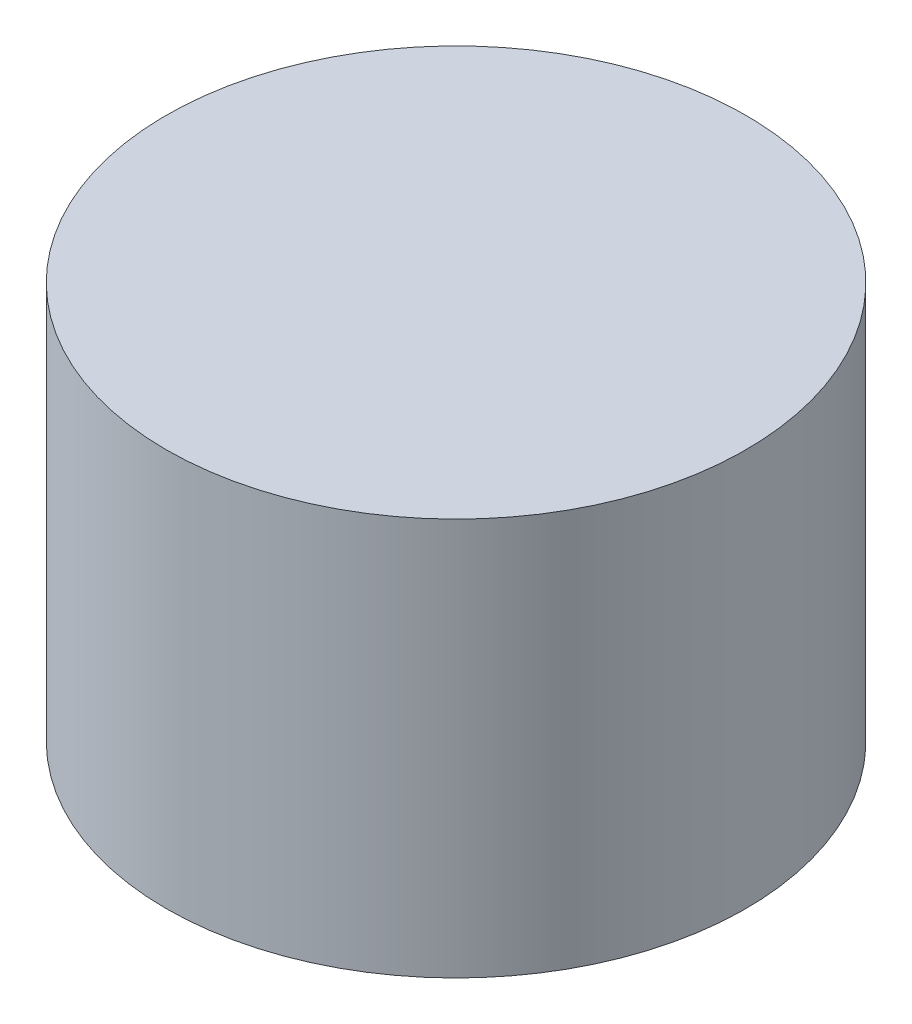
SolidWorks part; units mm, degrees
ref_plane "前视基准面" through (0, 0, 0) normal (0, 0, 1) x (1, 0, 0)
ref_plane "上视基准面" through (0, 0, 0) normal (0, 1, 0) x (1, 0, 0)
ref_plane "右视基准面" through (0, 0, 0) normal (1, 0, 0) x (0, 0, -1)
sketch "草图1" plane through (0, 0, 0) normal (0, 1, 0) x (1, 0, 0)
  circle A0 centre (0, 0) radius 52.5
  dimension "D1" = 105
extrude "凸台-拉伸1" add sketch "草图1" along normal blind 72
